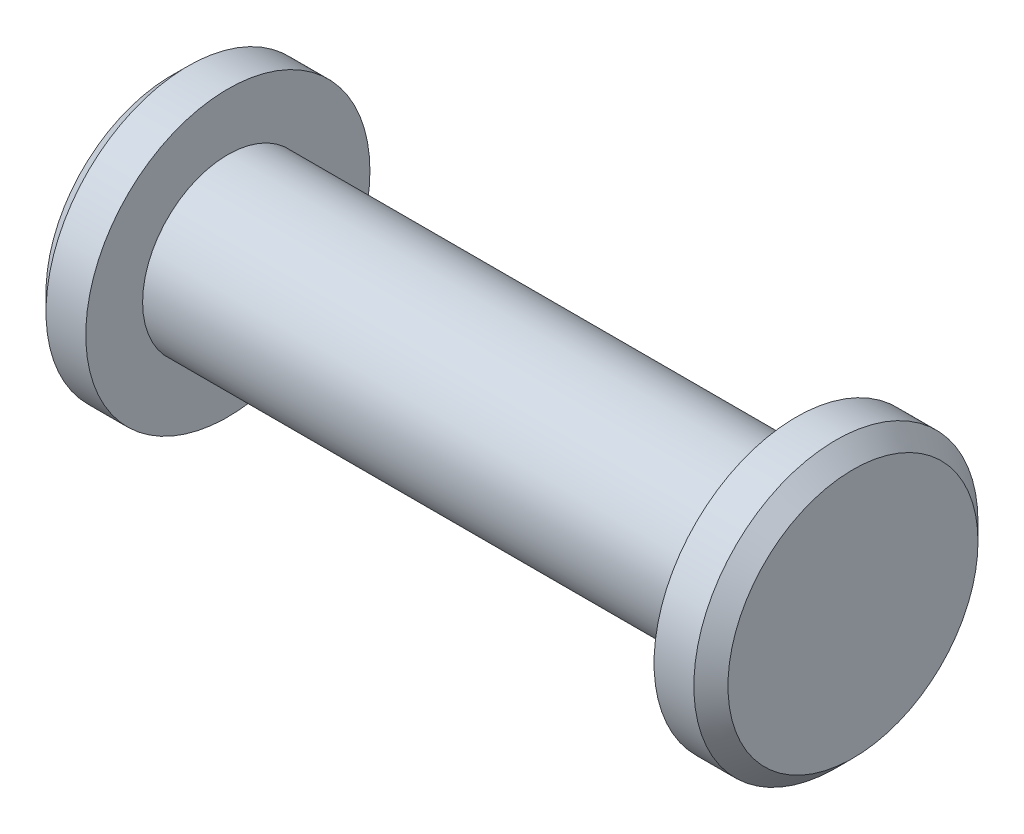
SolidWorks part; units mm, degrees
ref_plane "Front Plane" through (0, 0, 0) normal (0, 0, 1) x (1, 0, 0)
ref_plane "Top Plane" through (0, 0, 0) normal (0, 1, 0) x (1, 0, 0)
ref_plane "Right Plane" through (0, 0, 0) normal (1, 0, 0) x (0, 0, -1)
sketch "Sketch1" plane through (0, 0, 0) normal (0, 0, 1) x (1, 0, 0)
  line L0 (-50, 15) -> (50, 15)
  line L1 (50, 15) -> (50, 25)
  line L2 (50, 25) -> (57, 25)
  line L3 (57, 25) -> (60, 22)
  line L4 (60, 22) -> (60, 0)
  line L5 (60, 0) -> (-60, 0)
  line L6 (0, 0) -> (0, 32.2677) construction
  line L7 (-60, 22) -> (-60, 0)
  line L8 (-57, 25) -> (-60, 22)
  line L9 (-50, 25) -> (-57, 25)
  line L10 (-50, 15) -> (-50, 25)
  point P14 (0, 15)
  dimension "D1" = 50
  dimension "D2" = 10
  dimension "D3" = 45
  dimension "D4" = 3
  dimension "D5" = 15
  dimension "D6" = 25
revolve "Revolve1" add sketch "Sketch1" angle 360 about L5
